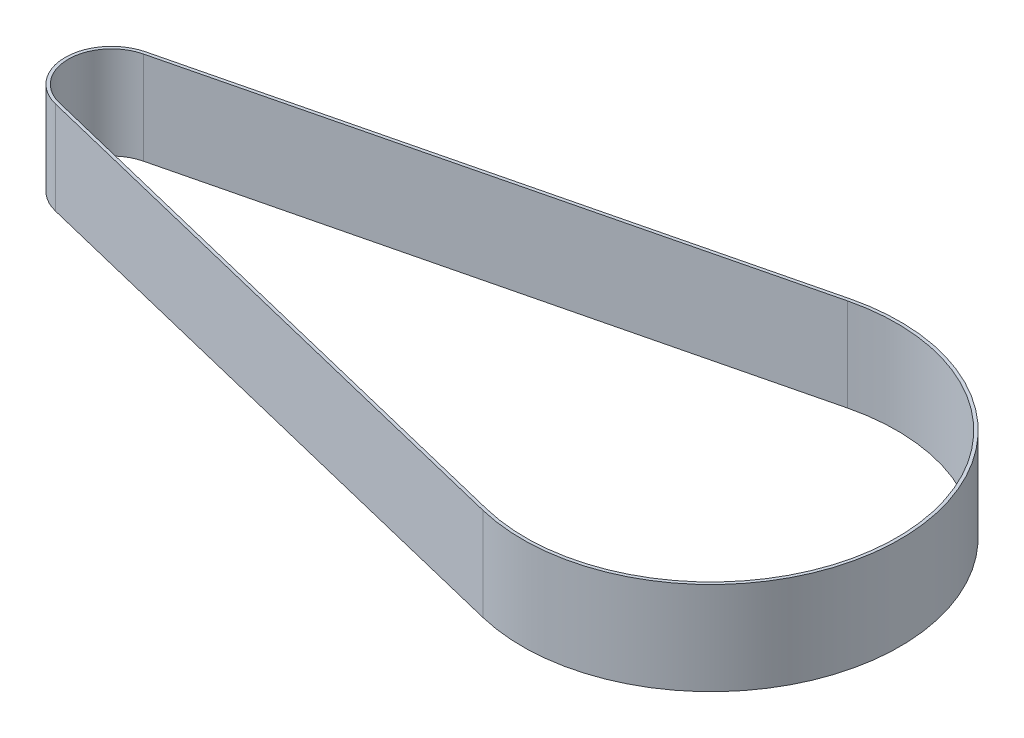
SolidWorks part; units mm, degrees
ref_plane "Front Plane" through (0, 0, 0) normal (0, 0, 1) x (1, 0, 0)
ref_plane "Top Plane" through (0, 0, 0) normal (0, 1, 0) x (1, 0, 0)
ref_plane "Right Plane" through (0, 0, 0) normal (1, 0, 0) x (0, 0, -1)
sketch "Sketch1" plane through (0, 0, 0) normal (0, 1, 0) x (1, 0, 0)
  line L8 (-274.0673, 129.1424) -> (-182.623, 151.4852)
  line L9 (-182.7417, 151.9709) -> (-274.1859, 129.6281)
  line L10 (-274.1859, 115.0568) -> (-182.7417, 92.714)
  line L11 (-182.623, 93.1997) -> (-274.0673, 115.5425)
  arc A8 (-182.623, 93.1997) -> (-182.623, 151.4852) centre (-175.5025, 122.3425) ccw
  arc A9 (-274.0673, 129.1424) -> (-274.0673, 115.5425) centre (-272.4058, 122.3425) ccw
  arc A10 (-274.1859, 129.6281) -> (-274.1859, 115.0568) centre (-272.4058, 122.3425) ccw
  arc A11 (-182.7417, 92.714) -> (-182.7417, 151.9709) centre (-175.5025, 122.3425) ccw
extrude "Boss-Extrude1" add sketch "Sketch1" along normal blind 15
